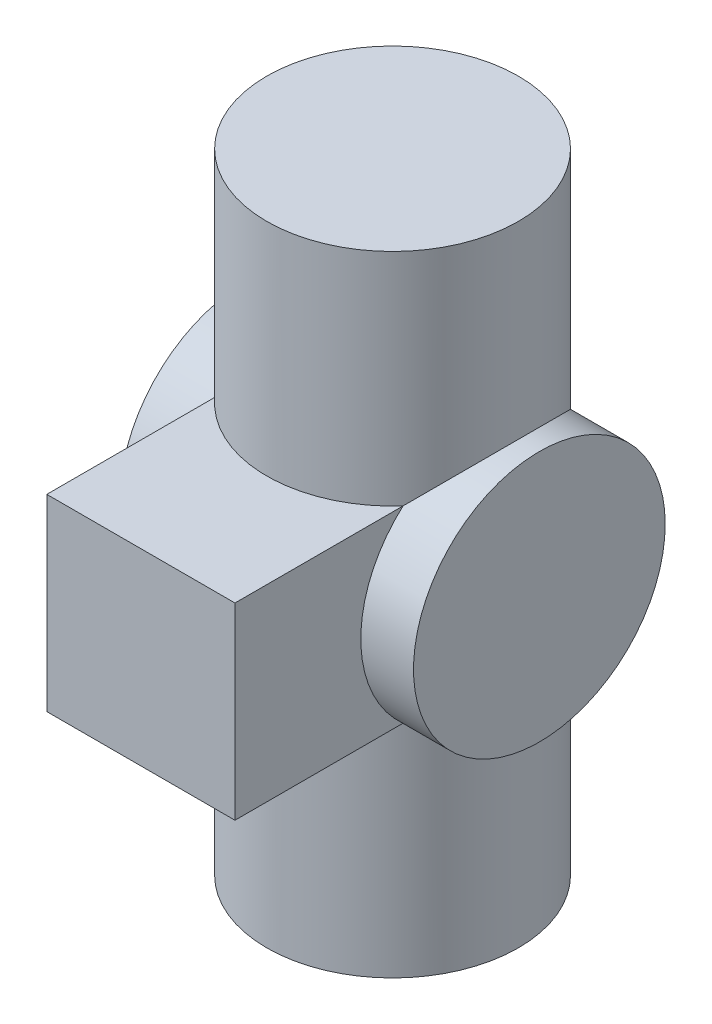
SolidWorks part; units mm, degrees
ref_plane "Front Plane" through (0, 0, 0) normal (0, 0, 1) x (1, 0, 0)
ref_plane "Top Plane" through (0, 0, 0) normal (0, 1, 0) x (1, 0, 0)
ref_plane "Right Plane" through (0, 0, 0) normal (1, 0, 0) x (0, 0, -1)
sketch "Sketch1" plane through (0, 0, 0) normal (0, 1, 0) x (1, 0, 0)
  circle A0 centre (0, 0) radius 30
extrude "Boss-Extrude1" add sketch "Sketch1" along normal blind 150 contours A0
sketch "Sketch3" plane through (0, 0, 0) normal (1, 0, 0) x (0, 0, -1)
  line L0 (0, 0) -> (0, 75)
  circle A0 centre (0, 75) radius 30
extrude "Boss-Extrude2" add sketch "Sketch3" along normal mid plane 70 contours A0
sketch "Sketch4" plane through (0, 0, 0) normal (0, 0, 1) x (1, 0, 0)
  line L1 (0, 97.4302) -> (22.4302, 97.4302)
  line L2 (0, 75) -> (30, 105) construction
  line L3 (22.4302, 97.4302) -> (22.4302, 52.5698)
  line L4 (0, 75) -> (30, 45) construction
  line L5 (22.4302, 52.5698) -> (-22.4302, 52.5698)
  line L6 (-30, 45) -> (0, 75) construction
  line L7 (-22.4302, 52.5698) -> (-22.4302, 97.4302)
  line L8 (-30, 105) -> (0, 75) construction
  line L9 (-22.4302, 97.4302) -> (0, 97.4302)
extrude "Boss-Extrude3" add sketch "Sketch4" along normal blind 60
